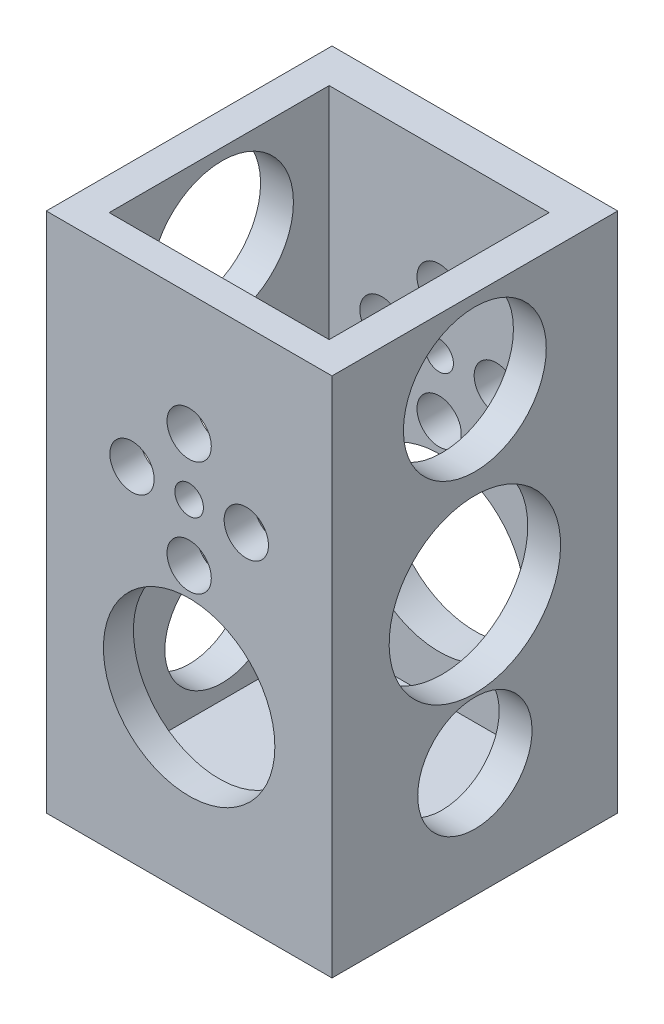
SolidWorks part; units mm, degrees
ref_plane "前视基准面" through (0, 0, 0) normal (0, 0, 1) x (1, 0, 0)
ref_plane "上视基准面" through (0, 0, 0) normal (0, 1, 0) x (1, 0, 0)
ref_plane "右视基准面" through (0, 0, 0) normal (1, 0, 0) x (0, 0, -1)
sketch "草图1" plane through (0, 0, 0) normal (0, 0, 1) x (1, 0, 0)
  line L0 (0, 0) -> (4, 0)
  line L1 (10, 0) -> (10, 12.5)
  line L2 (0, 12.5) -> (10, 12.5)
  line L3 (-10, 12.5) -> (-10, -24)
  line L4 (10, 0) -> (10, -24)
  line L5 (10, -24) -> (-10, -24)
  line L6 (0, 0) -> (0, 4)
  line L7 (0, 0) -> (0, -4)
  line L8 (0, 0) -> (-4, 0)
  line L9 (0, 0) -> (0, -19) construction
  line L25 (0, 12.5) -> (-10, 12.5)
  circle A0 centre (0, 0) radius 1
  circle A1 centre (0, 4) radius 1.55
  circle A2 centre (4, 0) radius 1.55
  circle A3 centre (0, -4) radius 1.55
  circle A4 centre (-4, 0) radius 1.55
  circle A5 centre (0, -11.9736) radius 6
extrude "凸台-拉伸1" add sketch "草图1" along normal blind 20
sketch "草图2" plane through (0, 12.5, 0) normal (0, 1, 0) x (1, 0, 0)
  line L1 (-10, 0) -> (10, 0) construction
  line L2 (-10, -20) -> (10, -20) construction
  line L3 (0, -20) -> (7.7, -20) construction
  line L4 (0, -20) -> (-11.1, -20) construction
  line L5 (-7.7, -10.2) -> (-7.7, -2.5)
  line L6 (-11.1, 0) -> (11.1, 0) construction
  line L7 (-7.7, -10.2) -> (-7.7, -17.9)
  line L8 (0, -17.9) -> (-7.7, -17.9)
  line L9 (7.7, -2.5) -> (7.7, -17.9)
  line L10 (0, -2.5) -> (7.7, -2.5)
  line L11 (7.7, -17.9) -> (0, -17.9)
  line L12 (0, -2.5) -> (-7.7, -2.5)
extrude "切除-拉伸1" cut sketch "草图2" against normal blind 33.5
sketch "草图3" plane through (-10, 0, 0) normal (-1, 0, 0) x (0, 0, 1)
  line L0 (10, 12.5) -> (10, -24)
  line L1 (20, 12.5) -> (0, 12.5) construction
  line L2 (20, -24) -> (0, -24) construction
  circle A0 centre (10, -5.75) radius 6
  circle A1 centre (10, 6.6881) radius 5
  circle A2 centre (10, -15.9731) radius 4
extrude "切除-拉伸2" cut sketch "草图3" against normal through all contours L0 A0 | L0 A0 | L0 A1 | L0 A1 | L0 A2 | L0 A2
